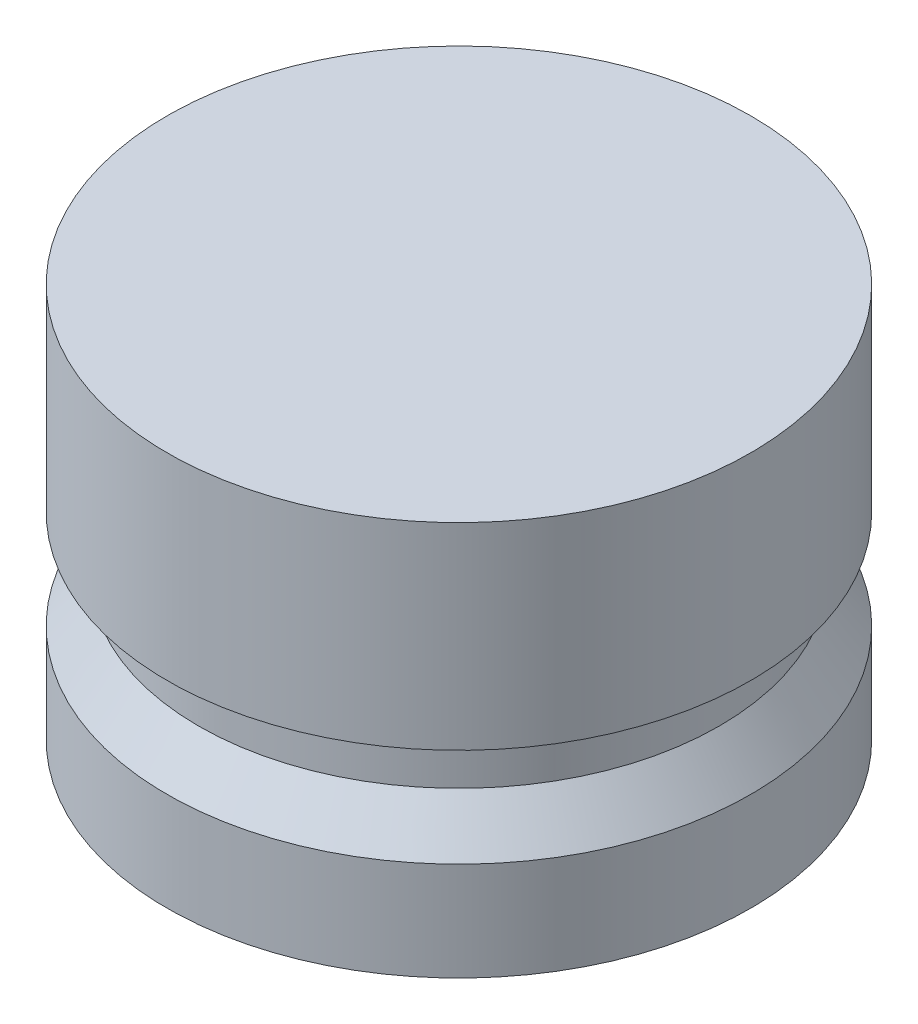
SolidWorks part; units mm, degrees
ref_plane "Front Plane" through (0, 0, 0) normal (0, 0, 1) x (1, 0, 0)
ref_plane "Top Plane" through (0, 0, 0) normal (0, 1, 0) x (1, 0, 0)
ref_plane "Right Plane" through (0, 0, 0) normal (1, 0, 0) x (0, 0, -1)
sketch "Sketch1" plane through (0, 0, 0) normal (0, 0, 1) x (1, 0, 0)
  line L0 (0, 0) -> (0, 12.7) construction
  line L1 (0, 0) -> (-9.398, 0)
  line L2 (-9.398, 0) -> (-9.398, 3.175)
  line L4 (-8.382, 4.572) -> (-8.382, 6.35)
  line L5 (-8.382, 6.35) -> (-9.398, 6.35)
  line L6 (-9.398, 6.35) -> (-9.398, 12.7)
  line L7 (-9.398, 12.7) -> (0, 12.7)
  line L8 (-9.525, 16.6801) -> (-9.525, -9.6051) construction
  line L9 (0, 0) -> (0, 12.7)
  line L10 (-8.382, 4.572) -> (-9.398, 3.175)
  dimension "D1" = 12.7
  dimension "D2" = 9.398
  dimension "D3" = 1.778
  dimension "D4" = 3.175
  dimension "D5" = 9.525
  dimension "D6" = 8.382
  dimension "D7" = 6.35
revolve "Revolve1" add sketch "Sketch1" angle 360 about L9
